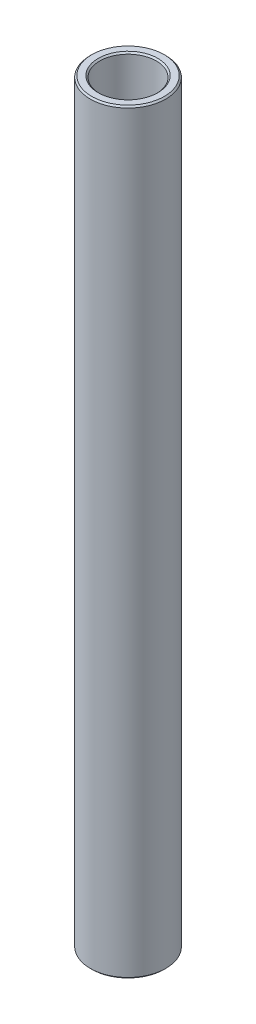
SolidWorks part; units mm, degrees
ref_plane "Front Plane" through (0, 0, 0) normal (0, 0, 1) x (1, 0, 0)
ref_plane "Top Plane" through (0, 0, 0) normal (0, 1, 0) x (1, 0, 0)
ref_plane "Right Plane" through (0, 0, 0) normal (1, 0, 0) x (0, 0, -1)
sketch "Sketch1" plane through (0, 0, 0) normal (0, 0, 1) x (1, 0, 0)
  line L0 (4.7625, 70.6437) -> (4.7625, 197.8308)
  line L1 (4.7625, 197.8308) -> (6.35, 197.8308)
  line L2 (6.35, 197.8308) -> (6.35, 70.6437)
  line L3 (6.35, 70.6437) -> (4.7625, 70.6437)
  line L4 (120.0875, 79.3749) -> (10.0875, 79.3749) construction
  line L6 (0, 61.1187) -> (0, 207.3558) construction
  dimension "D1" = 9.525
  dimension "D2" = 9.525
  dimension "D3" = 12.7
  dimension "D4" = 9.525
revolve "Revolve1" add sketch "Sketch1" angle 360 about L6
chamfer "Chamfer1" distance 0.254 angle 45 4 edges at (6.35, 197.8308, 0) (4.7625, 197.8308, 0) (4.7625, 70.6437, 0) (6.35, 70.6437, 0)
equation "\"D4@Sketch1\"=\"D1@Sketch1\""
